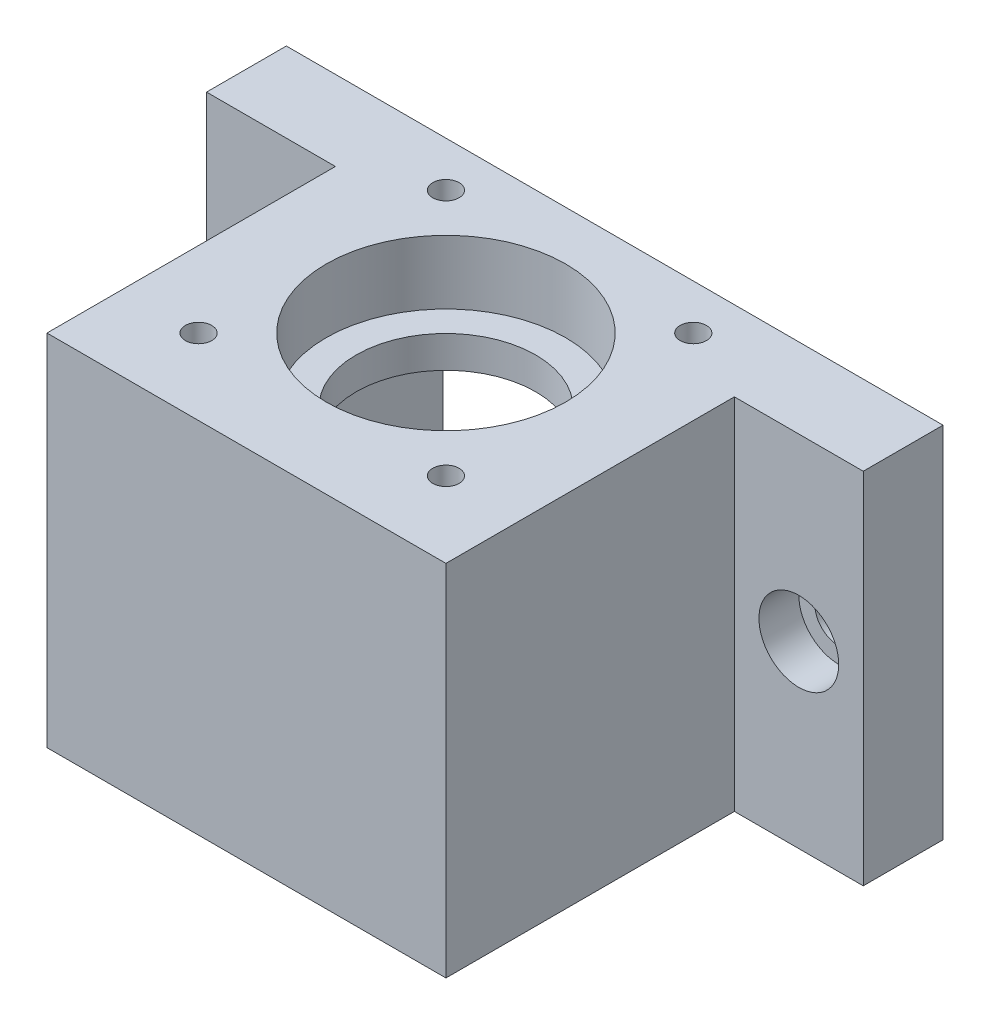
SolidWorks part; units mm, degrees
ref_plane "Спереди" through (0, 0, 0) normal (0, 0, 1) x (1, 0, 0)
ref_plane "Сверху" through (0, 0, 0) normal (0, 1, 0) x (1, 0, 0)
ref_plane "Справа" through (0, 0, 0) normal (1, 0, 0) x (0, 0, -1)
sketch "Эскиз1" plane through (0, 0, 0) normal (0, 1, 0) x (1, 0, 0)
  line L3 (-21.15, 21.15) -> (21.15, 21.15)
  line L6 (-25, 11.15) -> (-25, -25)
  line L7 (21.15, 21.15) -> (41.15, 21.15)
  line L8 (41.15, 21.15) -> (41.15, 11.15)
  line L9 (41.15, 11.15) -> (25, 11.15)
  line L10 (-21.15, 21.15) -> (-41.15, 21.15)
  line L11 (-41.15, 21.15) -> (-41.15, 11.15)
  line L12 (-41.15, 11.15) -> (-25, 11.15)
  line L13 (-25, -25) -> (25, -25)
  line L14 (25, 11.15) -> (25, -25)
  point P0 (0, 0)
  point P5 (0, 0)
  dimension "D3" = 20
  dimension "D4" = 10
  dimension "D5" = 20
  dimension "D6" = 10
extrude "Бобышка-Вытянуть1" add sketch "Эскиз1" along normal blind 45
sketch "Эскиз2" plane through (0, 0, 0) normal (0, -1, 0) x (1, 0, 0)
  line L0 (-21.5, 16.5) -> (-16.5, 21.5)
  line L1 (-21.5, -21.5) -> (21.5, -21.5)
  line L2 (-21.5, -21.5) -> (-21.5, 16.5)
  line L3 (-16.5, 21.5) -> (16.5, 21.5)
  line L4 (21.5, -21.5) -> (21.5, 16.5)
  line L5 (-21.5, -21.5) -> (21.5, 21.5) construction
  line L6 (-21.5, 21.5) -> (21.5, -21.5) construction
  line L7 (16.5, 21.5) -> (21.5, 16.5)
  point P0 (0, 0)
  dimension "D1" = 43
extrude "Вырез-Вытянуть1" cut sketch "Эскиз2" against normal blind 33
sketch "Эскиз3" plane through (0, 33, 0) normal (0, -1, 0) x (1, 0, 0)
  circle A0 centre (0, 0) radius 11.25
  dimension "D1" = 22.5
extrude "Вырез-Вытянуть2" cut sketch "Эскиз3" against normal through all
sketch "Эскиз4" plane through (0, 33, 0) normal (0, -1, 0) x (1, 0, 0)
  line L1 (15.5, -15.5) -> (-15.5, -15.5) construction
  line L2 (15.5, -15.5) -> (15.5, 15.5) construction
  line L3 (15.5, 15.5) -> (-15.5, 15.5) construction
  line L4 (-15.5, -15.5) -> (-15.5, 15.5) construction
  line L5 (15.5, -15.5) -> (-15.5, 15.5) construction
  line L6 (15.5, 15.5) -> (-15.5, -15.5) construction
  circle A0 centre (-15.5, 15.5) radius 1.65
  circle A1 centre (15.5, 15.5) radius 1.65
  circle A2 centre (-15.5, -15.5) radius 1.65
  circle A3 centre (15.5, -15.5) radius 1.65
  point P0 (0, 0)
  dimension "D2" = 3.3
  dimension "D3" = 3.3
  dimension "D4" = 3.3
  dimension "D5" = 3.3
  dimension "D1" = 31
extrude "Вырез-Вытянуть3" cut sketch "Эскиз4" against normal through all
sketch "Эскиз5" plane through (0, 0, -11.15) normal (0, 0, 1) x (1, 0, 0)
  circle A0 centre (-33.075, 22.5) radius 3
  circle A1 centre (33.075, 22.5) radius 3
  dimension "D1" = 6
  dimension "D2" = 6
extrude "Вырез-Вытянуть4" cut sketch "Эскиз5" against normal through all
sketch "Эскиз6" plane through (0, 0, -11.15) normal (0, 0, 1) x (1, 0, 0)
  circle A0 centre (-33.075, 22.5) radius 5
  circle A1 centre (33.075, 22.5) radius 5
  dimension "D1" = 10
  dimension "D2" = 10
extrude "Вырез-Вытянуть5" cut sketch "Эскиз6" against normal blind 5
sketch "Эскиз7" plane through (0, 45, 0) normal (0, 1, 0) x (1, 0, 0)
  circle A0 centre (0, 0) radius 15
  dimension "D1" = 30
extrude "Вырез-Вытянуть6" cut sketch "Эскиз7" against normal blind 8
